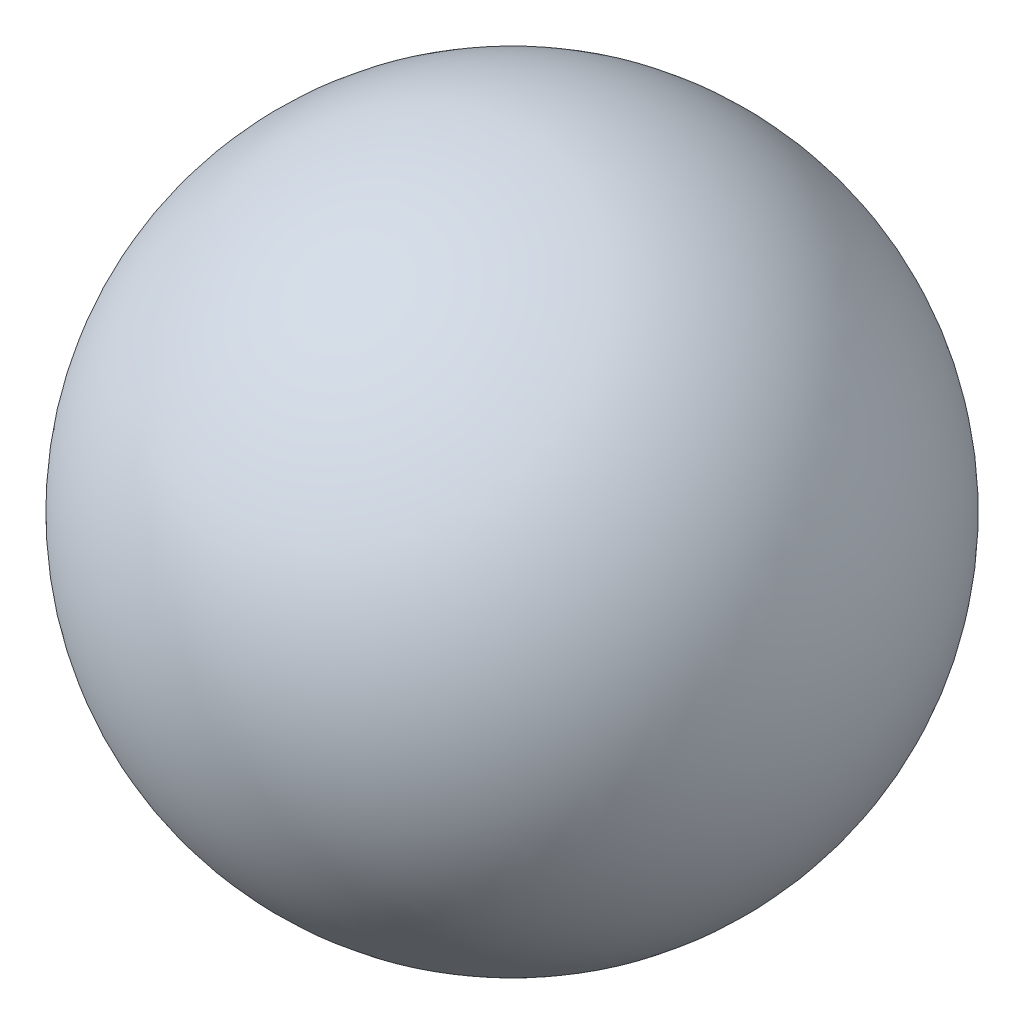
SolidWorks part; units mm, degrees
ref_plane "Ebene vorne" through (0, 0, 0) normal (0, 0, 1) x (1, 0, 0)
ref_plane "Ebene oben" through (0, 0, 0) normal (0, 1, 0) x (1, 0, 0)
ref_plane "Ebene rechts" through (0, 0, 0) normal (1, 0, 0) x (0, 0, -1)
sketch "Skizze1" plane through (0, 0, 0) normal (0, 0, 1) x (1, 0, 0)
  line L0 (-5, 0) -> (-5, 5)
  line L1 (-5, 5) -> (-2.5, 5)
  line L2 (-2.5, 5) -> (-2.5, 0)
  line L3 (2.5, 0) -> (2.5, 5)
  line L4 (2.5, 5) -> (5, 5)
  line L5 (-2.5, 5) -> (0, 5) construction
  line L6 (5, 5) -> (5, -5)
  line L7 (5, -5) -> (2.5, -5)
  line L8 (2.5, -5) -> (2.5, -4.3301)
  line L9 (-5, 0) -> (5, 0) construction
  line L10 (0, 5) -> (2.5, 5) construction
  line L11 (0, 5) -> (0, 0) construction
  arc A0 (-2.5, 0) -> (2.5, 0) centre (0, 0) ccw
  arc A1 (-5, 0) -> (2.5, -4.3301) centre (0, 0) ccw
  point P11 (0, -5)
  dimension "D1" = 10
extrude "Aufsatz-Linear austragen1" add sketch "Skizze1" along normal mid plane 5
sketch "Skizze2" plane through (0, 0, 0) normal (0, 0, 1) x (1, 0, 0)
  line L0 (0, 10) -> (0, -10)
  arc A0 (0, 10) -> (0, -10) centre (0, 0) ccw
  dimension "D1" = 20
revolve "Rotation1" add sketch "Skizze2" angle 360 about L0
